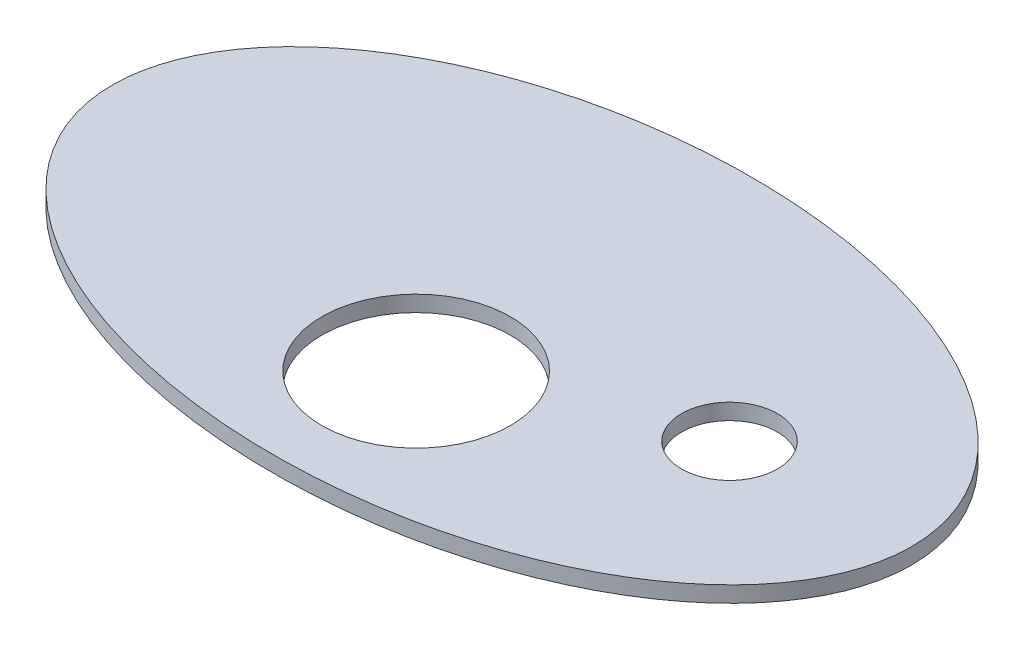
SolidWorks part; units mm, degrees
ref_plane "Front Plane" through (0, 0, 0) normal (0, 0, 1) x (1, 0, 0)
ref_plane "Top Plane" through (0, 0, 0) normal (0, 1, 0) x (1, 0, 0)
ref_plane "Right Plane" through (0, 0, 0) normal (1, 0, 0) x (0, 0, -1)
sketch "Sketch1" plane through (0, 0, 0) normal (0, 1, 0) x (1, 0, 0)
  ellipse E0 centre (0, 0) end of major axis (125, 0) minor radius 75
  point P1 (0, 0)
  point P7 (0, 0)
  point P9 (0, 0)
  dimension "D1" = 150
  dimension "D2" = 250
extrude "Boss-Extrude1" add sketch "Sketch1" along normal blind 5
sketch "Sketch2" plane through (0, 5, 0) normal (0, 1, 0) x (1, 0, 0)
  circle A0 centre (0, -30) radius 29.5
  circle A1 centre (68, 0) radius 15
  dimension "D3" = 30
  dimension "D4" = 59
  dimension "D1" = 30
  dimension "D2" = 68
extrude "Cut-Extrude1" cut sketch "Sketch2" against normal blind 5
